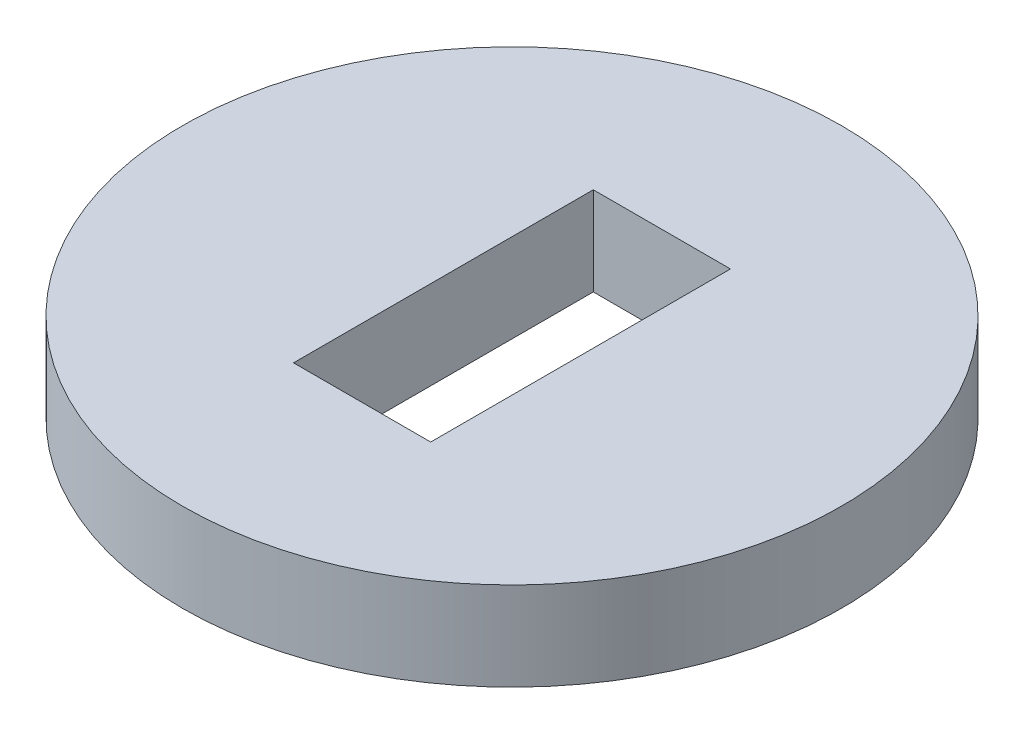
SolidWorks part; units mm, degrees
material "1060 Alloy"
ref_plane "Front Plane" through (0, 0, 0) normal (0, 0, 1) x (1, 0, 0)
ref_plane "Top Plane" through (0, 0, 0) normal (0, 1, 0) x (1, 0, 0)
ref_plane "Right Plane" through (0, 0, 0) normal (1, 0, 0) x (0, 0, -1)
sketch "Sketch1" plane through (0, 0, 0) normal (0, 1, 0) x (1, 0, 0)
  line L1 (-1.3716, 2.9972) -> (1.3716, 2.9972)
  line L2 (-1.3716, 2.9972) -> (-1.3716, -2.9972)
  line L3 (-1.3716, -2.9972) -> (1.3716, -2.9972)
  line L4 (1.3716, 2.9972) -> (1.3716, -2.9972)
  circle A0 centre (0, 0) radius 6.59
  point P7 (0, 2.9972)
  point P8 (-1.3716, 0)
  dimension "D1" = 13.18
  dimension "D2" = 5.9944
  dimension "D3" = 2.7432
extrude "Boss-Extrude1" add sketch "Sketch1" along normal blind 1.77
